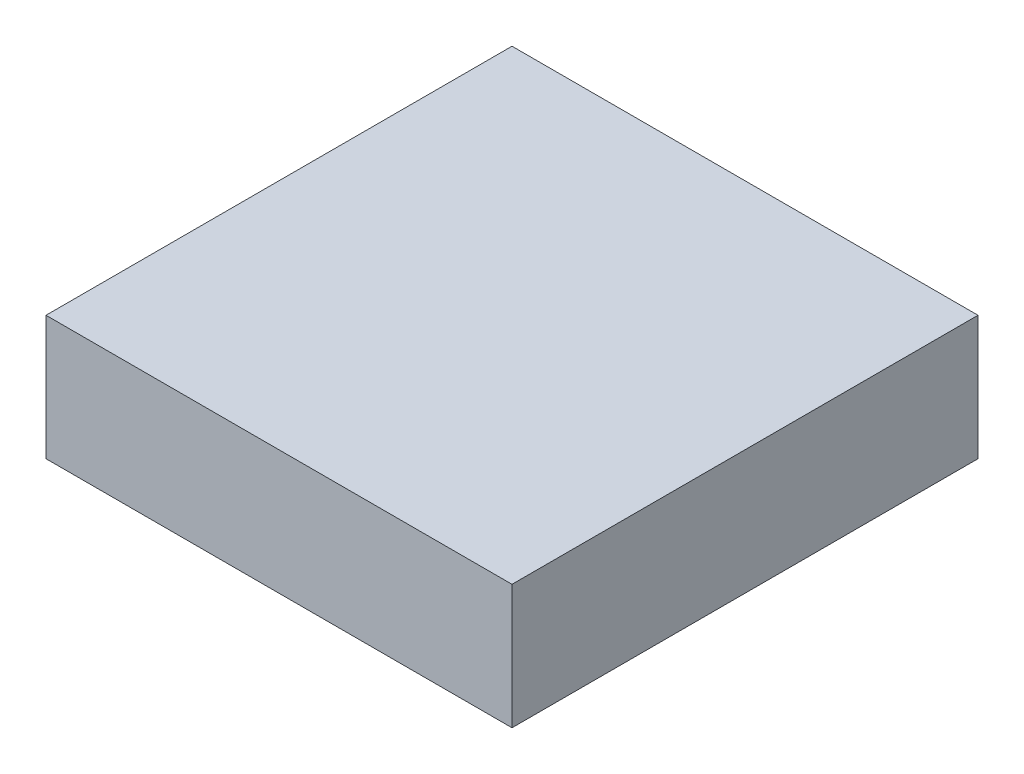
SolidWorks part; units mm, degrees
ref_plane "Front Plane" through (0, 0, 0) normal (0, 0, 1) x (1, 0, 0)
ref_plane "Top Plane" through (0, 0, 0) normal (0, 1, 0) x (1, 0, 0)
ref_plane "Right Plane" through (0, 0, 0) normal (1, 0, 0) x (0, 0, -1)
sketch "Sketch1" plane through (0, 0, 0) normal (0, 1, 0) x (1, 0, 0)
  line L1 (-38.1, 38.1) -> (38.1, 38.1)
  line L2 (-38.1, 38.1) -> (-38.1, -38.1)
  line L3 (-38.1, -38.1) -> (38.1, -38.1)
  line L4 (38.1, 38.1) -> (38.1, -38.1)
extrude "Boss-Extrude3" add sketch "Sketch1" along normal blind 20.32 contours L2 L3 L4 L1
shell "Shell3" thickness 2.54
